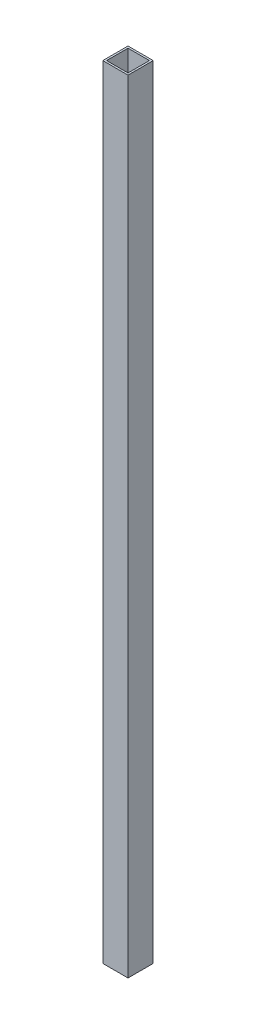
SolidWorks part; units mm, degrees
ref_plane "Front" through (0, 0, 0) normal (0, 0, 1) x (1, 0, 0)
ref_plane "Top" through (0, 0, 0) normal (0, 1, 0) x (1, 0, 0)
ref_plane "Right" through (0, 0, 0) normal (1, 0, 0) x (0, 0, -1)
sketch "Sketch1" plane through (0, 0, 0) normal (0, 1, 0) x (1, 0, 0)
  line L1 (20, -20) -> (-20, -20)
  line L2 (20, -20) -> (20, 20)
  line L3 (20, 20) -> (-20, 20)
  line L4 (-20, -20) -> (-20, 20)
  line L5 (20, -20) -> (-20, 20) construction
  line L6 (20, 20) -> (-20, -20) construction
  point P0 (0, 0)
  dimension "D1" = 40
  dimension "D2" = 40
extrude "Boss-Extrude1" add sketch "Sketch1" along normal blind 1240
sketch "Sketch2" plane through (0, 1240, 0) normal (0, 1, 0) x (1, 0, 0)
  line L1 (17, -17) -> (-17, -17)
  line L2 (17, -17) -> (17, 17)
  line L3 (17, 17) -> (-17, 17)
  line L4 (-17, -17) -> (-17, 17)
  line L5 (17, -17) -> (-17, 17) construction
  line L6 (17, 17) -> (-17, -17) construction
  point P0 (0, 0)
  dimension "D1" = 34
  dimension "D2" = 34
extrude "Cut-Extrude1" cut sketch "Sketch2" against normal through all
sketch "Sketch3" plane through (-20, 0, 0) normal (-1, 0, 0) x (0, 0, 1)
  line L0 (-20, 1220) -> (20, 1220) construction
  line L1 (-20, 1240) -> (-20, 0) construction
  line L2 (20, 1240) -> (20, 0) construction
  line L3 (-20, 1200) -> (20, 1200) construction
  line L4 (20, 1000) -> (-20, 1000) construction
  line L5 (20, 800) -> (-20, 800) construction
  line L6 (20, 600) -> (-20, 600) construction
  line L7 (-20, 1240) -> (20, 1240) construction
  dimension "D1" = 20
  dimension "D2" = 20
  dimension "D3" = 200
  dimension "D4" = 200
  dimension "D5" = 200
